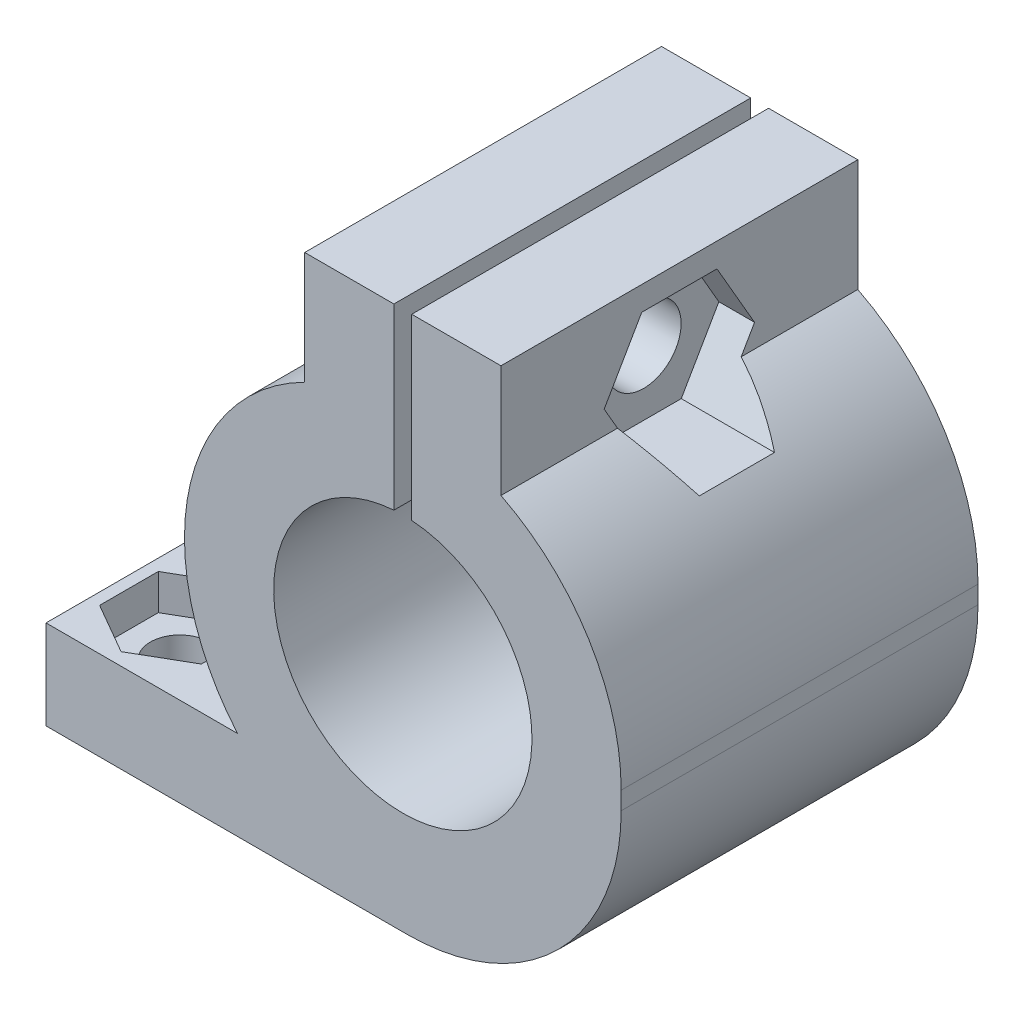
SolidWorks part; units mm, degrees
ref_plane "Front Plane" through (0, 0, 0) normal (0, 0, 1) x (1, 0, 0)
ref_plane "Top Plane" through (0, 0, 0) normal (0, 1, 0) x (1, 0, 0)
ref_plane "Right Plane" through (0, 0, 0) normal (1, 0, 0) x (0, 0, -1)
sketch "Sketch1" plane through (0, 0, 0) normal (0, 0, 1) x (1, 0, 0)
  line L0 (-20, -13) -> (20, -13) construction
  line L1 (0, 0) -> (0, 6.35) construction
  line L2 (-0.5, 0) -> (-0.5, 7.2217) construction
  line L3 (0.5, 0) -> (0.5, 7.2217) construction
  line L4 (-0.5, 7.2217) -> (-0.5, 17.2317)
  line L5 (0.5, 7.2217) -> (0.5, 17.2317)
  line L6 (-0.5, 17.2317) -> (-5.5, 17.2317)
  line L7 (-5.5, 17.2317) -> (-5.5, 10.9336)
  line L8 (-9.2625, -8) -> (9.2625, -8) construction
  line L9 (5.5, 17.2317) -> (5.5, 10.9336)
  line L10 (0.5, 17.2317) -> (5.5, 17.2317)
  line L11 (-9.2625, -8) -> (-20, -8)
  line L12 (-20, -8) -> (-20, -13)
  line L15 (-12.239, 0) -> (-12.239, -8) construction
  line L16 (12.239, 0) -> (12.239, -13)
  line L17 (12.239, -13) -> (-20, -13)
  arc A0 (-0.5, 7.2217) -> (0.5, 7.2217) centre (0, 0) ccw
  circle A1 centre (0, 0) radius 6.35 construction
  arc A2 (-0.5, 17.2317) -> (0.5, 17.2317) centre (0, 0) ccw construction
  arc A3 (12.239, 0) -> (9.2625, -8) centre (0, 0) ccw construction
  arc A4 (-5.5, 10.9336) -> (-9.2625, -8) centre (0, 0) ccw
  arc A5 (5.5, 10.9336) -> (12.239, 0) centre (0, 0) cw
  point P7 (0, -13)
  point P20 (0, -8)
  dimension "D1" = 14.478
  dimension "D2" = 12.7
  dimension "D5" = 10
  dimension "D7" = 5
  dimension "D3" = 13
  dimension "D4" = 0.5
  dimension "D6" = 5
  dimension "D8" = 5
  dimension "D9" = 40
extrude "Boss-Extrude1" add sketch "Sketch1" along normal blind 20
sketch "Sketch2" plane through (-5.5, 0, 0) normal (-1, 0, 0) x (0, 0, 1)
  line L0 (0, 0) -> (20, 0) construction
  line L1 (20, -8) -> (20, 10.9336) construction
  line L2 (10, 0) -> (10, 17.2317) construction
  line L3 (20, 17.2317) -> (0, 17.2317) construction
  line L5 (12.1073, 15.8817) -> (7.8927, 15.8817) construction
  line L6 (7.8927, 15.8817) -> (5.7853, 12.2317) construction
  line L7 (5.7853, 12.2317) -> (7.8927, 8.5817) construction
  line L8 (7.8927, 8.5817) -> (12.1073, 8.5817) construction
  line L9 (12.1073, 8.5817) -> (14.2147, 12.2317) construction
  line L10 (14.2147, 12.2317) -> (12.1073, 15.8817) construction
  circle A0 centre (10, 12.2317) radius 2.1
  circle A1 centre (10, 12.2317) radius 3.65 construction
  circle A2 centre (10, 12.2317) radius 3.65 construction
  dimension "D1" = 4.2
  dimension "D2" = 7.3
  dimension "D3" = 3.65
  dimension "D4" = 5
extrude "Cut-Extrude1" cut sketch "Sketch2" against normal through all both and the other way through all
sketch "Sketch4" plane through (-5.5, 0, 0) normal (-1, 0, 0) x (0, 0, 1)
  circle A0 centre (10, 12.2317) radius 3.65 construction
  circle A1 centre (10, 12.2317) radius 3.65
extrude "Cut-Extrude2" cut sketch "Sketch4" along normal through all and the other way blind 2
sketch "Sketch5" plane through (5.5, 0, 0) normal (1, 0, 0) x (0, 0, -1)
  line L0 (-12.1073, 8.5817) -> (-14.2147, 12.2317) construction
  line L1 (-7.8927, 8.5817) -> (-12.1073, 8.5817) construction
  line L2 (-5.7853, 12.2317) -> (-7.8927, 8.5817) construction
  line L3 (-7.8927, 15.8817) -> (-5.7853, 12.2317) construction
  line L4 (-12.1073, 15.8817) -> (-7.8927, 15.8817) construction
  line L5 (-14.2147, 12.2317) -> (-12.1073, 15.8817) construction
  line L6 (-12.1073, 8.5817) -> (-14.2147, 12.2317)
  line L7 (-7.8927, 8.5817) -> (-12.1073, 8.5817)
  line L8 (-5.7853, 12.2317) -> (-7.8927, 8.5817)
  line L9 (-7.8927, 15.8817) -> (-5.7853, 12.2317)
  line L10 (-12.1073, 15.8817) -> (-7.8927, 15.8817)
  line L11 (-14.2147, 12.2317) -> (-12.1073, 15.8817)
extrude "Cut-Extrude3" cut sketch "Sketch5" along normal through all and the other way blind 2
sketch "Sketch6" plane through (0, -8, 0) normal (0, 1, 0) x (1, 0, 0)
  line L0 (-20, -10) -> (0, -10) construction
  line L1 (-20, -20) -> (-20, 0) construction
  line L2 (0, -10) -> (0, 0) construction
  circle A0 centre (-16.5, -4) radius 1.65
  circle A1 centre (-16.5, -16) radius 1.65
  circle A2 centre (16.5, -16) radius 1.65 construction
  circle A3 centre (16.5, -4) radius 1.65 construction
  circle A4 centre (-16.5, -4) radius 2.85 construction
  dimension "D2" = 3.3
  dimension "D5" = 5.7
  dimension "D1" = 6
  dimension "D3" = 16.5
  dimension "D4" = 3.5
extrude "Cut-Extrude4" cut sketch "Sketch6" against normal through all
sketch "Sketch7" plane through (0, -8, 0) normal (0, 1, 0) x (1, 0, 0)
  line L1 (-16.5, -7.2909) -> (-13.65, -5.6454)
  line L2 (-13.65, -5.6454) -> (-13.65, -2.3546)
  line L3 (-13.65, -2.3546) -> (-16.5, -0.7091)
  line L4 (-16.5, -0.7091) -> (-19.35, -2.3546)
  line L5 (-19.35, -2.3546) -> (-19.35, -5.6454)
  line L6 (-19.35, -5.6454) -> (-16.5, -7.2909)
  line L7 (-16.5, -12.7091) -> (-19.35, -14.3546)
  line L8 (-19.35, -14.3546) -> (-19.35, -17.6454)
  line L9 (-19.35, -17.6454) -> (-16.5, -19.2909)
  line L10 (-16.5, -19.2909) -> (-13.65, -17.6454)
  line L11 (-13.65, -17.6454) -> (-13.65, -14.3546)
  line L12 (-13.65, -14.3546) -> (-16.5, -12.7091)
  circle A0 centre (-16.5, -4) radius 2.85 construction
  circle A1 centre (-16.5, -4) radius 2.85 construction
  circle A2 centre (-16.5, -16) radius 2.85 construction
  circle A3 centre (16.5, -4) radius 2.85 construction
  circle A4 centre (16.5, -16) radius 2.85 construction
  circle A5 centre (-16.5, -4) radius 2.85 construction
  circle A6 centre (-16.5, -16) radius 2.85 construction
extrude "Cut-Extrude5" cut sketch "Sketch7" against normal blind 2
fillet "Fillet1" radius 12 1 edges at (12.239, -13, 10)
